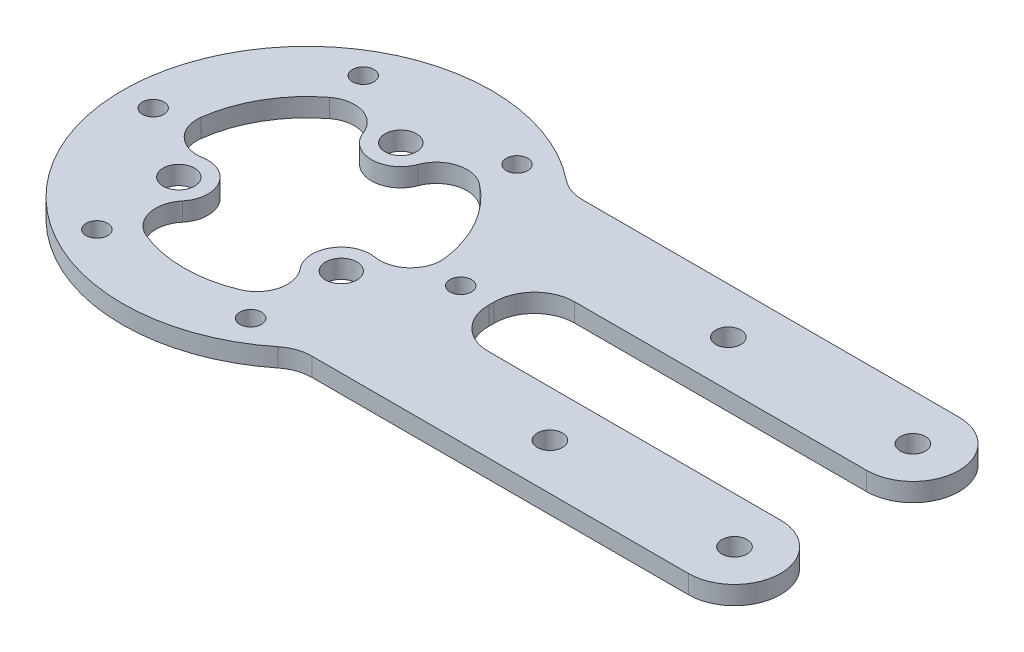
SolidWorks part; units mm, degrees
ref_plane "Front Plane" through (0, 0, 0) normal (0, 0, 1) x (1, 0, 0)
ref_plane "Top Plane" through (0, 0, 0) normal (0, 1, 0) x (1, 0, 0)
ref_plane "Right Plane" through (0, 0, 0) normal (1, 0, 0) x (0, 0, -1)
sketch "Sketch1" plane through (0, 0, 0) normal (0, 1, 0) x (1, 0, 0)
  circle A0 centre (0, 0) radius 30
  circle A4 centre (0, 0) radius 20
  dimension "D1" = 60
  dimension "D2" = 10
extrude "Boss-Extrude1" add sketch "Sketch1" along normal blind 3
sketch "Sketch2" plane through (0, 3, 0) normal (0, 1, 0) x (1, 0, 0)
  line L0 (-4.75, 15.25) -> (-4.75, 19.4278)
  line L1 (4.75, 15.25) -> (4.75, 19.4278)
  circle A0 centre (0, 0) radius 15.25 construction
  circle A1 centre (0, 15.25) radius 2.55
  arc A2 (-4.75, 15.25) -> (4.75, 15.25) centre (0, 15.25) ccw
  circle A3 centre (0, 0) radius 20 construction
  arc A4 (-4.75, 19.4278) -> (4.75, 19.4278) centre (0, 0) cw
  dimension "D1" = 30.5
  dimension "D2" = 5.1
  dimension "D3" = 2.2
extrude "Boss-Extrude2" add sketch "Sketch2" against normal up to surface (3 mm away) up to face at (0, 0, 30)
pattern_circular "CirPattern1" count 3 over 360 about axis through (0, 0, 0) along (0, 1, 0) of "Boss-Extrude2"
sketch "Sketch3" plane through (0, 3, 0) normal (0, 1, 0) x (1, 0, 0)
  line L1 (20.3961, 22) -> (99, 22)
  line L3 (29.1719, 7) -> (99, 7)
  line L4 (99, 22) -> (99, 7)
  line L5 (29.1719, -7) -> (99, -7)
  line L7 (20.3961, -22) -> (99, -22)
  line L8 (99, -7) -> (99, -22)
  line L9 (19.2614, 23) -> (100, 23) construction
  line L11 (29.3939, 6) -> (100, 6) construction
  line L12 (100, 23) -> (100, 6) construction
  line L13 (29.3939, -6) -> (100, -6) construction
  line L15 (19.2614, -23) -> (100, -23) construction
  line L16 (100, -6) -> (100, -23) construction
  circle A0 centre (0, 0) radius 30 construction
  arc A1 (19.2614, 23) -> (29.3939, 6) centre (0, 0) cw construction
  arc A2 (29.3939, -6) -> (19.2614, -23) centre (0, 0) cw construction
  arc A3 (20.3961, 22) -> (29.1719, 7) centre (0, 0) cw
  arc A4 (29.1719, -7) -> (20.3961, -22) centre (0, 0) cw
  dimension "D1" = 12
  dimension "D2" = 100
  dimension "D3" = 6
  dimension "D4" = 17
  dimension "D5" = 1
  dimension "D6" = 1
  dimension "D7" = 1
  dimension "D8" = 1
  dimension "D9" = 1
extrude "Boss-Extrude3" add sketch "Sketch3" against normal up to surface (3 mm away) up to face at (0, 0, 30)
sketch "Sketch4" plane through (0, 3, 0) normal (0, 1, 0) x (1, 0, 0)
  line L0 (99, 7) -> (99, 22) construction
  line L1 (54, 14.5) -> (84, 14.5) construction
  line L2 (54, 14.5) -> (54, -14.5) construction
  line L3 (54, -14.5) -> (84, -14.5) construction
  line L4 (84, 14.5) -> (84, -14.5) construction
  line L5 (99, -22) -> (99, -7) construction
  circle A0 centre (54, 14.5) radius 2.05
  circle A1 centre (84, 14.5) radius 2.05
  circle A2 centre (54, -14.5) radius 2.05
  circle A3 centre (84, -14.5) radius 2.05
  point P10 (99, 14.5)
  point P13 (99, -14.5)
  dimension "D1" = 4.1
  dimension "D2" = 30
  dimension "D3" = 15
extrude "Cut-Extrude1" cut sketch "Sketch4" against normal through all
sketch "Sketch6" plane through (0, 0, 0) normal (0, -1, 0) x (1, 0, 0)
  circle A0 centre (0, 0) radius 25 construction
  circle A1 centre (25, 0) radius 1.75
  point P5 (0, 0)
  dimension "D1" = 50
  dimension "D2" = 3.5
extrude "Cut-Extrude2" cut sketch "Sketch6" against normal through all
pattern_circular "CirPattern2" count 6 over 360 about axis through (0, 0, 0) along (0, 1, 0) of "Cut-Extrude2"
sketch "Sketch7" plane through (0, 0, 0) normal (0, -1, 0) x (1, 0, 0)
  line L1 (99, 22) -> (84, 22)
  line L2 (99, 22) -> (99, 7)
  line L3 (99, 7) -> (84, 7)
  line L5 (99, -7) -> (84, -7)
  line L6 (99, -7) -> (99, -22)
  line L7 (99, -22) -> (84, -22)
  arc A0 (84, 7) -> (84, 22) centre (84, 14.5) ccw
  arc A1 (84, -22) -> (84, -7) centre (84, -14.5) ccw
extrude "Cut-Extrude3" cut sketch "Sketch7" against normal through all
fillet "Fillet1" radius 5 6 edges at (19.1999, 1.5, 5.6003) (14.4499, 1.5, 13.8275) (-19.1999, 1.5, 5.6003) (-14.4499, 1.5, 13.8275) (4.75, 1.5, -19.4278) (-4.75, 1.5, -19.4278)
fillet "Fillet2" radius 6.5 4 edges at (20.3961, 1.5, -22) (29.1719, 1.5, -7) (29.1719, 1.5, 7) (20.3961, 1.5, 22)
